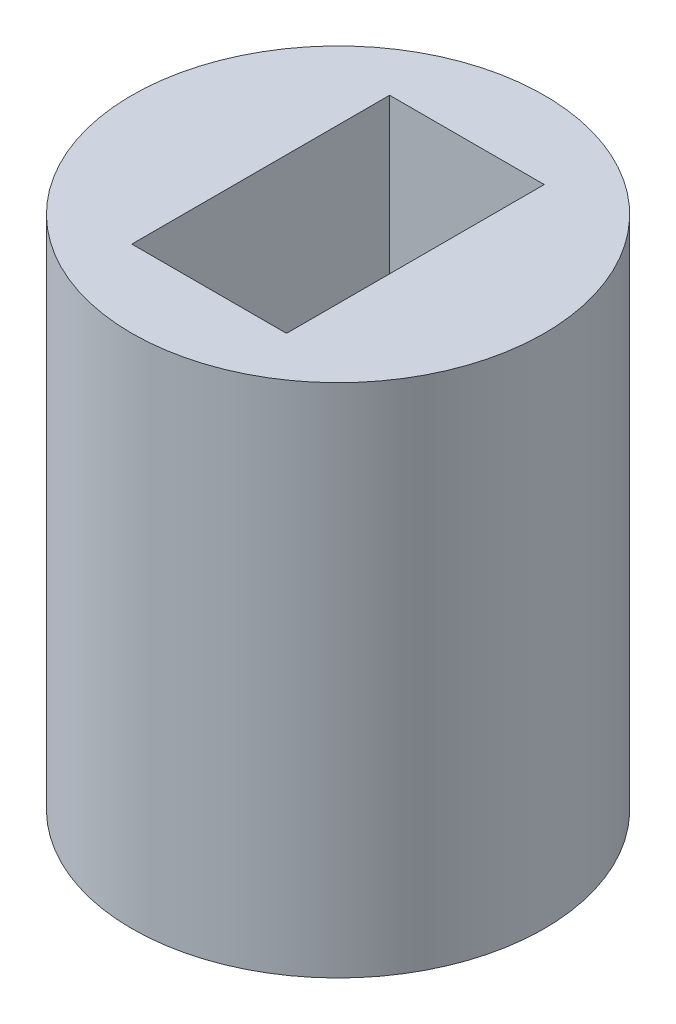
SolidWorks part; units mm, degrees
ref_plane "Front Plane" through (0, 0, 0) normal (0, 0, 1) x (1, 0, 0)
ref_plane "Top Plane" through (0, 0, 0) normal (0, 1, 0) x (1, 0, 0)
ref_plane "Right Plane" through (0, 0, 0) normal (1, 0, 0) x (0, 0, -1)
sketch "Sketch1" plane through (0, 0, 0) normal (0, 1, 0) x (1, 0, 0)
  line L1 (0, -4) -> (0, 4) construction
  line L2 (-1.5, 2.5) -> (1.5, 2.5)
  line L3 (-1.5, 2.5) -> (-1.5, -2.5)
  line L4 (-1.5, -2.5) -> (1.5, -2.5)
  line L5 (1.5, 2.5) -> (1.5, -2.5)
  circle A0 centre (0, 0) radius 4
  dimension "D1" = 8
  dimension "D2" = 3
  dimension "D3" = 5
  dimension "D4" = 1.5
  dimension "D5" = 2.5
extrude "Boss-Extrude1" add sketch "Sketch1" along normal blind 10
